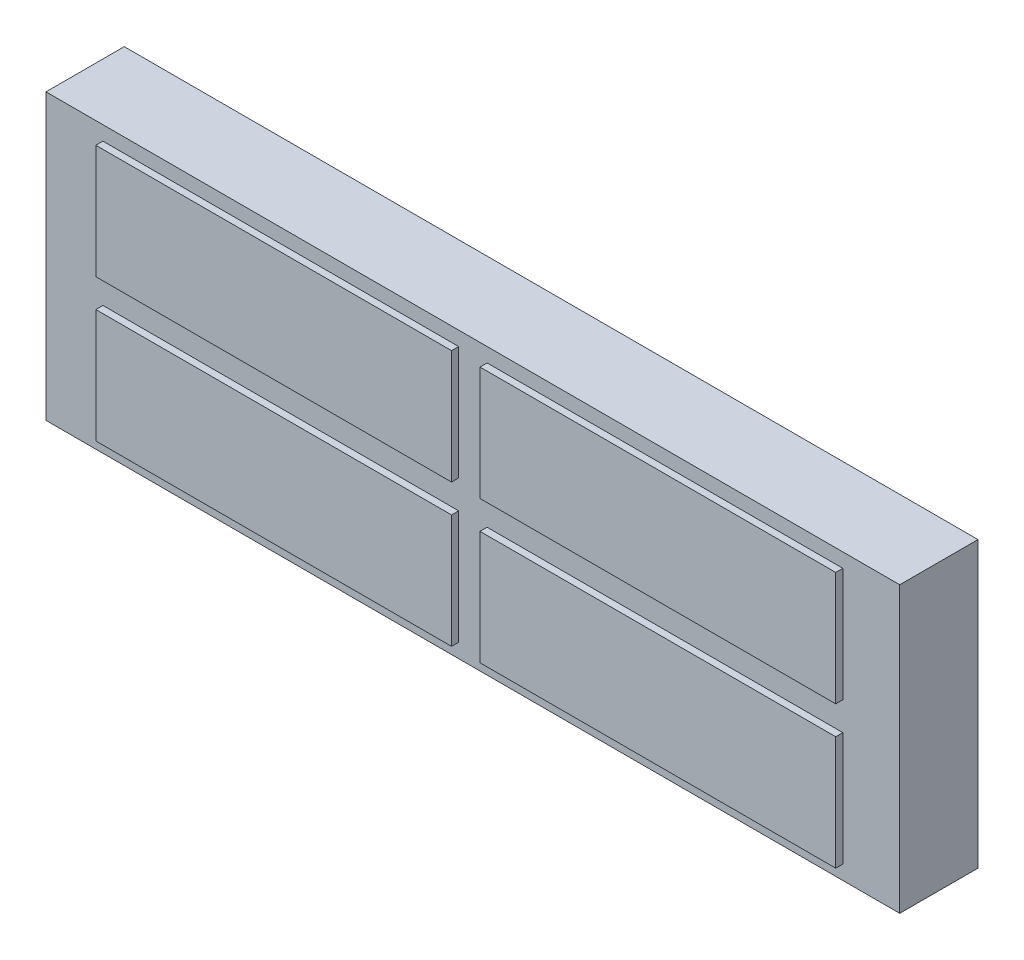
SolidWorks part; units mm, degrees
ref_plane "Plan de face" through (0, 0, 0) normal (0, 0, 1) x (1, 0, 0)
ref_plane "Plan de dessus" through (0, 0, 0) normal (0, 1, 0) x (1, 0, 0)
ref_plane "Plan de droite" through (0, 0, 0) normal (1, 0, 0) x (0, 0, -1)
sketch "Esquisse1" plane through (0, 0, 0) normal (0, 0, 1) x (1, 0, 0)
  line L1 (0, 0) -> (-60, 0)
  line L2 (0, 0) -> (0, 20)
  line L3 (0, 20) -> (-60, 20)
  line L4 (-60, 0) -> (-60, 20)
  dimension "D1" = 20
  dimension "D2" = 60
extrude "Extrusion1" add sketch "Esquisse1" along normal blind 5.5
sketch "Esquisse2" plane through (0, 0, 5.5) normal (0, 0, 1) x (1, 0, 0)
  line L0 (-60, 20) -> (-60, 0) construction
  line L1 (-56, 19) -> (-31, 19)
  line L2 (-56, 19) -> (-56, 11)
  line L3 (-56, 11) -> (-31, 11)
  line L4 (-31, 19) -> (-31, 11)
  line L5 (-56, 9) -> (-31, 9)
  line L6 (-56, 9) -> (-56, 1)
  line L7 (-56, 1) -> (-31, 1)
  line L8 (-31, 9) -> (-31, 1)
  line L9 (-29, 19) -> (-4, 19)
  line L10 (-29, 19) -> (-29, 11)
  line L11 (-29, 11) -> (-4, 11)
  line L12 (-4, 19) -> (-4, 11)
  line L13 (-29, 9) -> (-4, 9)
  line L14 (-29, 9) -> (-29, 1)
  line L15 (-29, 1) -> (-4, 1)
  line L16 (-4, 9) -> (-4, 1)
  line L17 (0, 0) -> (0, 20) construction
  line L18 (-60, 0) -> (0, 0) construction
  line L19 (0, 20) -> (-60, 20) construction
  dimension "D1" = 25
  dimension "D2" = 4
  dimension "D3" = 8
  dimension "D4" = 4
  dimension "D5" = 1
  dimension "D6" = 1
extrude "Extrusion2" add sketch "Esquisse2" along normal blind 0.5
